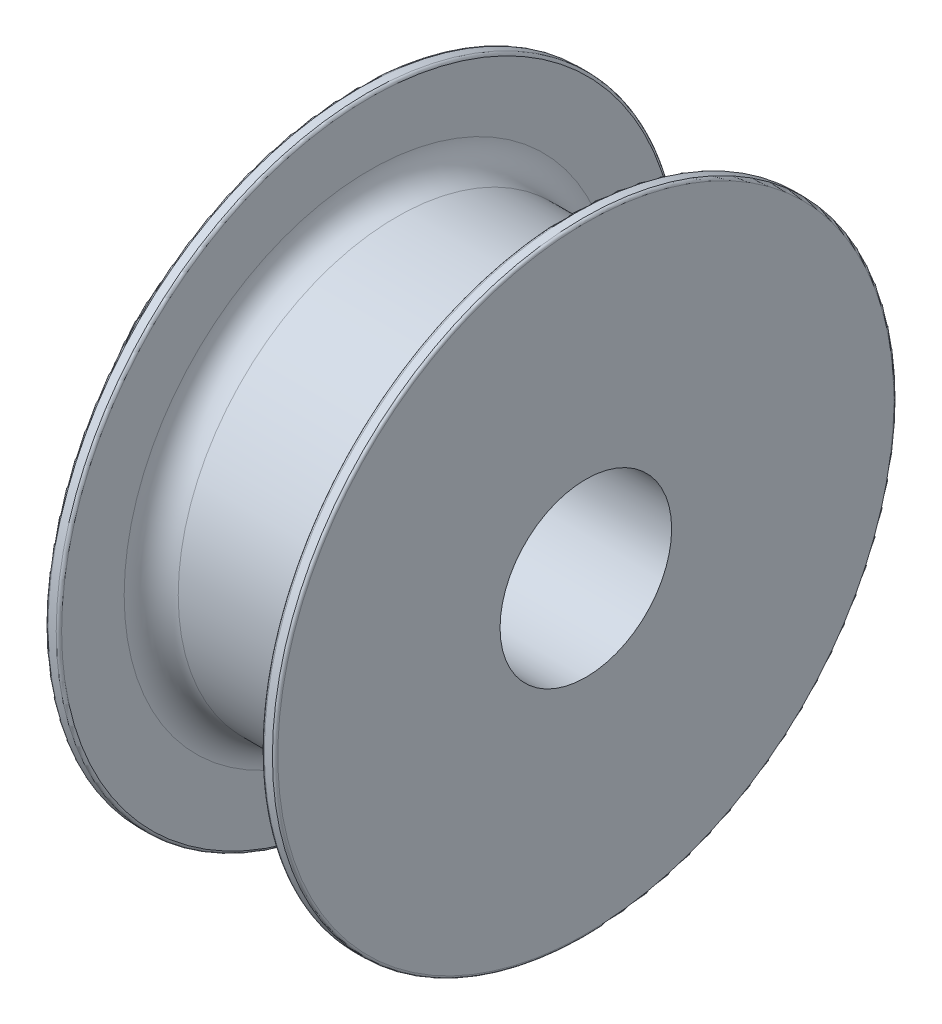
SolidWorks part; units mm, degrees
ref_plane "Front Plane" through (0, 0, 0) normal (0, 0, 1) x (1, 0, 0)
ref_plane "Top Plane" through (0, 0, 0) normal (0, 1, 0) x (1, 0, 0)
ref_plane "Right Plane" through (0, 0, 0) normal (1, 0, 0) x (0, 0, -1)
sketch "Sketch1" plane through (0, 0, 0) normal (1, 0, 0) x (0, 0, -1)
  circle A0 centre (0, 0) radius 16.1702
  circle A1 centre (0, 0) radius 6.35
  dimension "D1" = 32.3403
extrude "Boss-Extrude1" add sketch "Sketch1" along normal blind 15
sketch "Sketch2" plane through (15, 0, 0) normal (1, 0, 0) x (0, 0, -1)
  circle A0 centre (0, 0) radius 23
  circle A1 centre (0, 0) radius 6.35
extrude "Boss-Extrude2" add sketch "Sketch2" along normal blind 1
sketch "Sketch3" plane through (0, 0, 0) normal (-1, 0, 0) x (0, 0, 1)
  circle A0 centre (0, 0) radius 23
  circle A1 centre (0, 0) radius 6.35
extrude "Boss-Extrude3" add sketch "Sketch3" along normal blind 1
fillet "Fillet1" radius 2 2 edges at (0, 0, 16.1702) (15, 0, -16.1702)
fillet "Fillet2" radius 0.2 4 edges at (16, 0, -23) (-1, 0, 23) (0, 0, 23) (15, 0, -23)
sketch "Sketch4" plane through (-1, 0, 0) normal (-1, 0, 0) x (0, 0, 1)
  circle A0 centre (0, 0) radius 6.35
  circle A1 centre (0, 0) radius 12.5
extrude "Boss-Extrude4" add sketch "Sketch4" along normal blind 7.5
sketch "Sketch5" plane through (0, 0, 0) normal (0, 0, 1) x (1, 0, 0)
  circle A0 centre (-4.4323, 0) radius 3.175
extrude "Cut-Extrude1" cut sketch "Sketch5" against normal blind 17.5
fillet "Fillet3" radius 0.2 1 edges at (-8.5, 0, 12.5)
